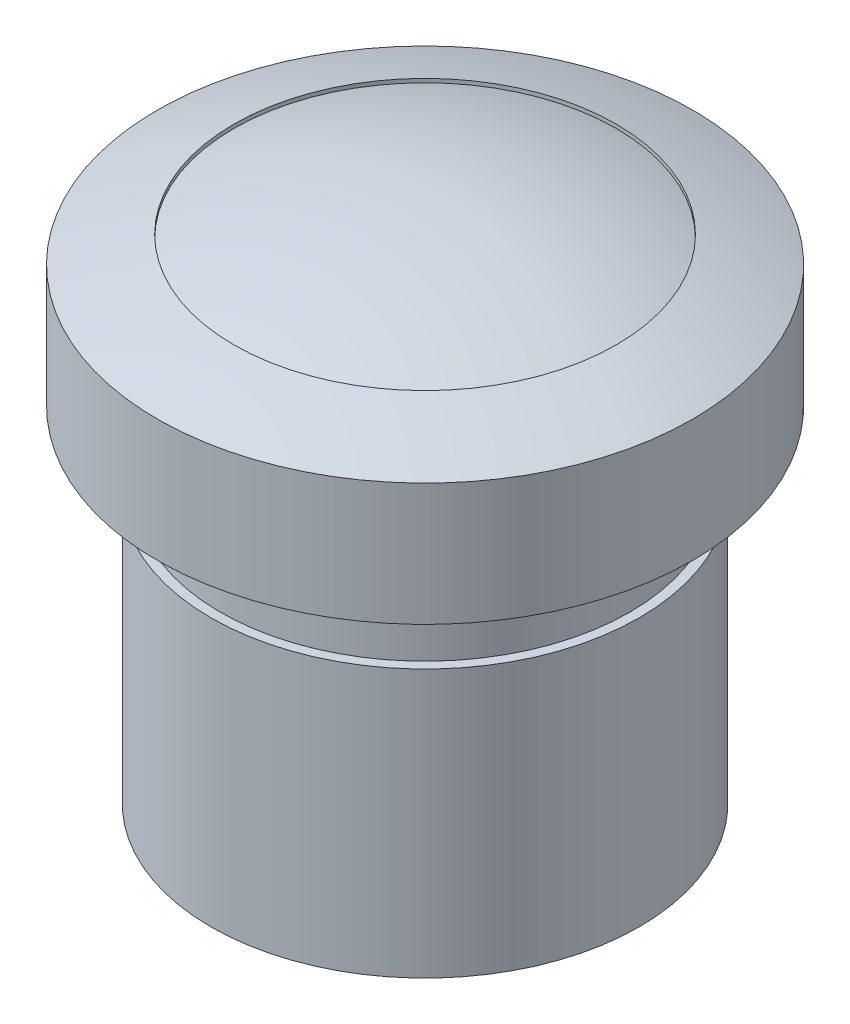
SolidWorks part; units mm, degrees
ref_plane "Front Plane" through (0, 0, 0) normal (0, 0, 1) x (1, 0, 0)
ref_plane "Top Plane" through (0, 0, 0) normal (0, 1, 0) x (1, 0, 0)
ref_plane "Right Plane" through (0, 0, 0) normal (1, 0, 0) x (0, 0, -1)
sketch "Sketch1" plane through (0, 0, 0) normal (0, 1, 0) x (1, 0, 0)
  circle A0 centre (0, 0) radius 5.6
  dimension "D1" = 11.2
extrude "Boss-Extrude1" add sketch "Sketch1" along normal blind 9
sketch "Sketch2" plane through (0, 0, 0) normal (0, 0, 1) x (1, 0, 0)
  line L0 (0, 9) -> (0, 13.7)
  line L1 (5.6, 9) -> (-5.6, 9) construction
  line L2 (0, 9) -> (-7, 9)
  line L3 (-7, 9) -> (-7, 12.2)
  line L4 (0, 13.7) -> (-11.0525, 13.7) construction
  line L5 (-5.6, 0) -> (5.6, 0) construction
  line L6 (-5, 12.8812) -> (-5, 12.7812)
  arc A0 (-7, 12.2) -> (-5, 12.8812) centre (0.8416, -7.547) cw
  arc A1 (-5, 12.7812) -> (0, 13.7) centre (0, -0.3638) cw
  dimension "D1" = 7
  dimension "D2" = 3.2
  dimension "D3" = 13.7
  dimension "D4" = 2
  dimension "D5" = 0.1
revolve "Revolve1" add sketch "Sketch2" angle 360 about L0
ref_plane "Plane1" through (0, 13.7, 0) normal (0, 1, 0) x (1, 0, 0)
sketch "Sketch4" plane through (0, 9, 0) normal (0, -1, 0) x (1, 0, 0)
  circle A0 centre (0, 0) radius 5.35
  circle A1 centre (0, 0) radius 5.6 construction
  circle A2 centre (0, 0) radius 5.6
  dimension "D1" = 10.7
extrude "Cut-Extrude1" cut sketch "Sketch4" along normal blind 2
sketch "Sketch5" plane through (0, 0, 0) normal (0, -1, 0) x (1, 0, 0)
  circle A2 centre (0, 0) radius 5.4
  circle A3 centre (0, 0) radius 5.4
  dimension "D1" = 0.2
extrude "Cut-Extrude3" cut sketch "Sketch5" against normal offset from surface (6 mm away) 1 up to face at (5.6, 7, 0)
sketch "Sketch6" plane through (0, 0, 0) normal (0, -1, 0) x (1, 0, 0)
  line L0 (3.2912, -4.2811) -> (1.6601, -2.65)
  line L1 (1.6601, -2.65) -> (-1.6601, -2.65)
  line L2 (2.65, -1.6601) -> (2.65, 1.6601)
  line L3 (1.6601, 2.65) -> (-1.6601, 2.65)
  line L4 (-2.65, -1.6601) -> (-2.65, 1.6601)
  line L5 (2.65, -2.65) -> (-2.65, 2.65) construction
  line L6 (2.65, 2.65) -> (-2.65, -2.65) construction
  line L7 (4.2811, -3.2912) -> (2.65, -1.6601)
  line L8 (-2.65, -1.6601) -> (-4.2811, -3.2912)
  line L9 (-1.6601, -2.65) -> (-3.2912, -4.2811)
  line L10 (2.65, 1.6601) -> (4.2811, 3.2912)
  line L11 (1.6601, 2.65) -> (3.2912, 4.2811)
  line L13 (-1.6601, 2.65) -> (-3.2912, 4.2811)
  line L14 (-2.65, 1.6601) -> (-4.2811, 3.2912)
  circle A0 centre (0, 0) radius 5.4 construction
  circle A1 centre (0, 0) radius 5.4 construction
  arc A2 (-3.2912, 4.2811) -> (-4.2811, 3.2912) centre (0, 0) ccw
  arc A3 (-4.2811, -3.2912) -> (-3.2912, -4.2811) centre (0, 0) ccw
  arc A4 (3.2912, -4.2811) -> (4.2811, -3.2912) centre (0, 0) ccw
  arc A5 (4.2811, 3.2912) -> (3.2912, 4.2811) centre (0, 0) ccw
  point P0 (0, 0)
  point P13 (-0.495, -0.495)
  point P14 (0.495, 0.495)
  dimension "D1" = 5.3
  dimension "D2" = 1.4
  dimension "D3" = 1.4
extrude "Boss-Extrude2" add sketch "Sketch6" against normal up to surface (6 mm away) up to face at (5.4, 6, 0)
sketch "Sketch7" plane through (0, 0, 0) normal (0, -1, 0) x (1, 0, 0)
  line L1 (2.25, -2.25) -> (-2.25, -2.25)
  line L2 (2.25, -2.25) -> (2.25, 2.25)
  line L3 (2.25, 2.25) -> (-2.25, 2.25)
  line L4 (-2.25, -2.25) -> (-2.25, 2.25)
  line L5 (2.25, -2.25) -> (-2.25, 2.25) construction
  line L6 (2.25, 2.25) -> (-2.25, -2.25) construction
  point P0 (0, 0)
  dimension "D1" = 4.5
extrude "Cut-Extrude4" cut sketch "Sketch7" against normal blind 0.8
sketch "Sketch8" plane through (0, 0.8, 0) normal (0, -1, 0) x (1, 0, 0)
  circle A0 centre (0, 0) radius 1.75
  dimension "D1" = 3.5
extrude "Cut-Extrude5" cut sketch "Sketch8" against normal blind 1
sketch "Sketch9" plane through (0, 0, 0) normal (0, 0, 1) x (1, 0, 0)
  line L0 (-1.75, 1.8) -> (1.75, 1.8) construction
  line L1 (-1.75, 1.8) -> (1.75, 1.8) construction
  line L2 (-1.75, 0.8) -> (1.75, 0.8) construction
  line L3 (-1.75, 0.8) -> (1.75, 0.8) construction
  line L4 (0, 0.8) -> (0, 1.8)
  line L5 (0, 1.8) -> (-1.75, 1.8)
  arc A1 (0, 0.8) -> (-1.75, 1.8) centre (0, 2.8312) cw
revolve "Revolve2" add sketch "Sketch9" angle 360 about L4
